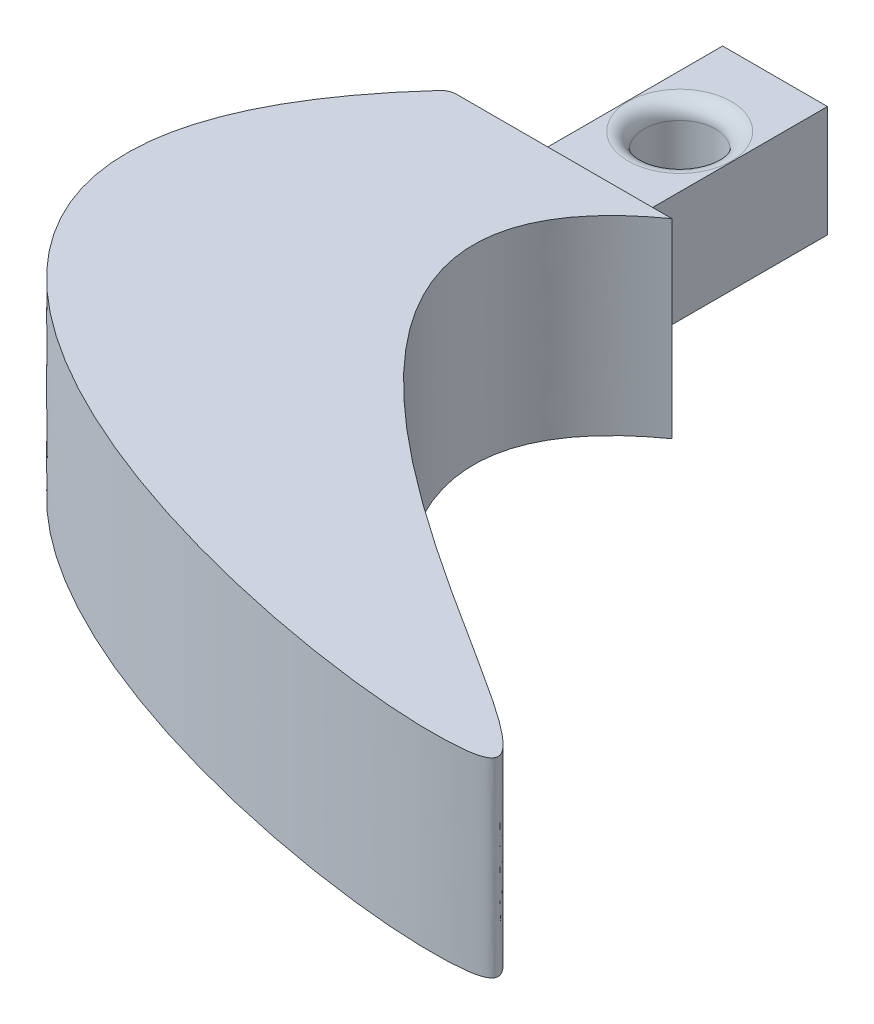
SolidWorks part; units mm, degrees
ref_plane "前视基准面" through (0, 0, 0) normal (0, 0, 1) x (1, 0, 0)
ref_plane "上视基准面" through (0, 0, 0) normal (0, 1, 0) x (1, 0, 0)
ref_plane "右视基准面" through (0, 0, 0) normal (1, 0, 0) x (0, 0, -1)
sketch "草图1" plane through (0, 0, 0) normal (0, 0, 1) x (1, 0, 0)
  line L0 (-5.3, 0.0072) -> (5.9626, 0.0072) construction
  line L1 (2.9918, -3.9928) -> (-4.0082, -3.9928)
  line L2 (2.9918, -3.9928) -> (2.9918, 3.0072)
  line L3 (2.9918, 3.0072) -> (-4.0082, 3.0072)
  line L4 (-4.0082, -3.9928) -> (-4.0082, 3.0072)
  line L5 (2.9918, -3.9928) -> (-4.0082, 3.0072) construction
  line L6 (2.9918, 3.0072) -> (-4.0082, -3.9928) construction
  line L7 (0, -5.2292) -> (0, 5.0744) construction
  dimension "D1" = 7
  dimension "D2" = 7
extrude "凸台-拉伸1" add sketch "草图1" along normal blind 14
sketch "草图3" plane through (0, 0, 14) normal (0, 0, 1) x (1, 0, 0)
  line L7 (-9.6508, 0) -> (9.1774, 0) construction
  line L8 (0, 0) -> (0, 14.4751) construction
ref_plane "基准面1" through (0, 0, 0) normal (0, 1, 0) x (1, 0, 0)
sketch "草图6" plane through (0, 0, 0) normal (0, 1, 0) x (1, 0, 0)
  line L0 (-7, -14) -> (7, -14)
  line L1 (-9.6508, -14) -> (9.1774, -14) construction
  spline S0 degree 3 poles (-7, -14) (-31.4959, -40.3702) (23.119, -51.4871) (36.0352, -47.7315) (-11.6769, -27.3191) (7, -14) knots 0 0 0 0 0.550644 0.609171 1 1 1 1
  point P5 (0, -14)
  dimension "D1" = 14
  dimension "D2" = 7
sketch3d "3D草图1"
  point P0 (0, 0, 14)
extrude "凸台-拉伸2" add sketch "草图6" along normal mid plane 12
sketch "草图15" plane through (0, 3.0072, 0) normal (0, 1, 0) x (1, 0, 0)
  line L0 (2.9918, -14) -> (-4.0082, -14) construction
  line L1 (2.9918, -14) -> (2.9918, 0) construction
  circle A0 centre (-0.5082, -6) radius 2.25
  dimension "D1" = 4.5
  dimension "D2" = 8
  dimension "D3" = 3.5
extrude "切除-拉伸2" cut sketch "草图15" against normal mid plane 12
fillet "圆角3" radius 1 1 edges at (-7, 0, 14)
sketch "草图16" plane through (0, 3.0072, 0) normal (0, 1, 0) x (1, 0, 0)
  line L0 (-9.6508, -14) -> (9.1774, -14) construction
  line L1 (2.9918, 0) -> (2.7918, 0)
  line L2 (2.9918, 0) -> (2.9918, -14)
  line L3 (2.9918, -14) -> (2.7918, -14)
  line L4 (2.7918, 0) -> (2.7918, -14)
  line L5 (-0.5082, 0) -> (-0.5082, -14)
  line L6 (2.9918, 0) -> (-4.0082, 0) construction
  line L7 (-3.8082, 0) -> (-3.8082, -14)
  line L8 (-4.0082, -14) -> (-3.8082, -14)
  line L9 (-4.0082, 0) -> (-4.0082, -14)
  line L10 (-4.0082, 0) -> (-3.8082, 0)
  line M4 (2.9918, 0) -> (-4.0082, 0)
  line M5 (-4.0082, 0) -> (-4.0082, -14)
  line M6 (-4.0082, -14) -> (2.9918, -14)
  dimension "D1" = 0.2
extrude "切除-拉伸3" cut sketch "草图16" against normal blind 10 contours L7 M4 M5 M6 | L4 L3 L2 L1
sketch "草图17" plane through (0, -2.9928, 0) normal (0, 1, 0) x (1, 0, 0)
  circle A0 centre (-0.5082, -6) radius 2.25 construction
  circle A1 centre (-0.5082, -6) radius 2.25
extrude "切除-拉伸4" cut sketch "草图17" against normal blind 10
fillet "圆角4" radius 1 2 edges at (-2.7582, -3.9928, 6) (1.7418, 3.0072, 6)
